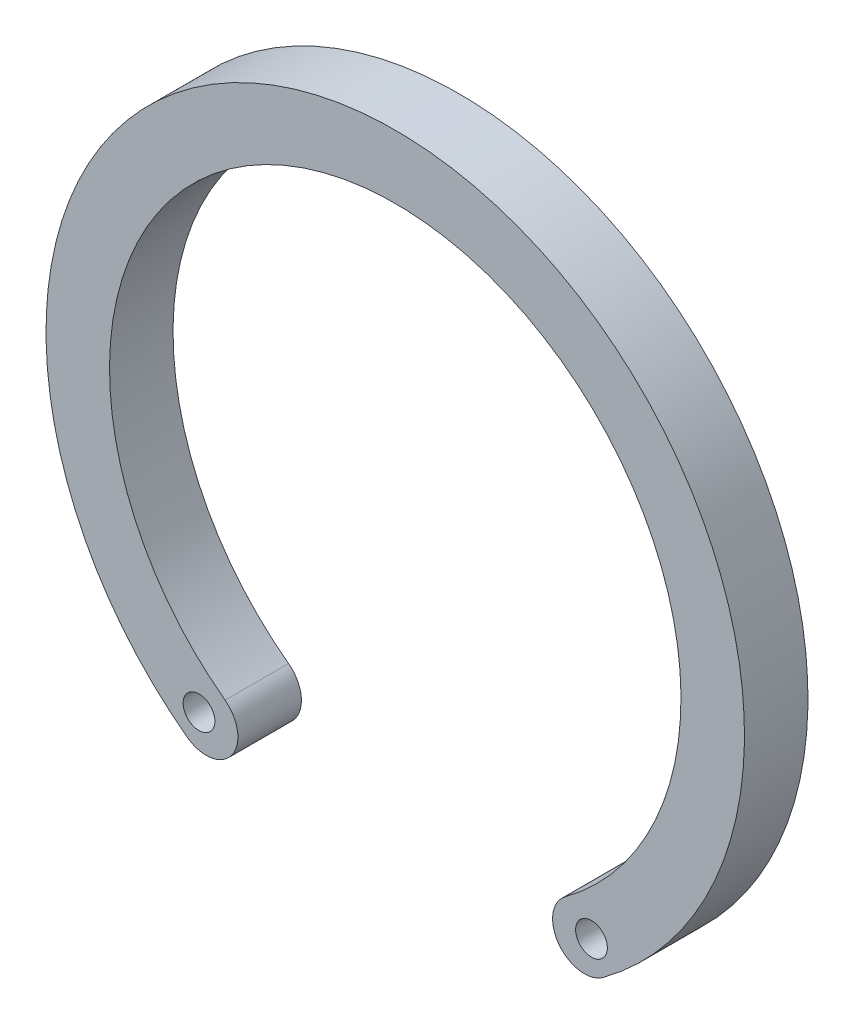
SolidWorks part; units mm, degrees
ref_plane "Front Plane" through (0, 0, 0) normal (0, 0, 1) x (1, 0, 0)
ref_plane "Top Plane" through (0, 0, 0) normal (0, 1, 0) x (1, 0, 0)
ref_plane "Right Plane" through (0, 0, 0) normal (1, 0, 0) x (0, 0, -1)
sketch "Sketch1" plane through (0, 0, 0) normal (0, 0, 1) x (1, 0, 0)
  arc A0 (2.68, -3.6149) -> (-2.68, -3.6149) centre (0, 0) ccw
  arc A1 (3.2756, -4.4182) -> (-3.2756, -4.4182) centre (0, 0) ccw
  arc A2 (-3.2756, -4.4182) -> (-2.68, -3.6149) centre (-2.9778, -4.0166) ccw
  arc A3 (3.2756, -4.4182) -> (2.68, -3.6149) centre (2.9778, -4.0166) cw
  dimension "D1" = 9
  dimension "D2" = 11
extrude "Boss-Extrude1" add sketch "Sketch1" along normal blind 1
sketch "Sketch2" plane through (0, 0, 1) normal (0, 0, 1) x (1, 0, 0)
  circle A0 centre (-3.0905, -3.9842) radius 0.25
  circle A1 centre (3.0905, -3.9842) radius 0.25
  dimension "D1" = 0.5
extrude "Cut-Extrude1" cut sketch "Sketch2" against normal blind 1
